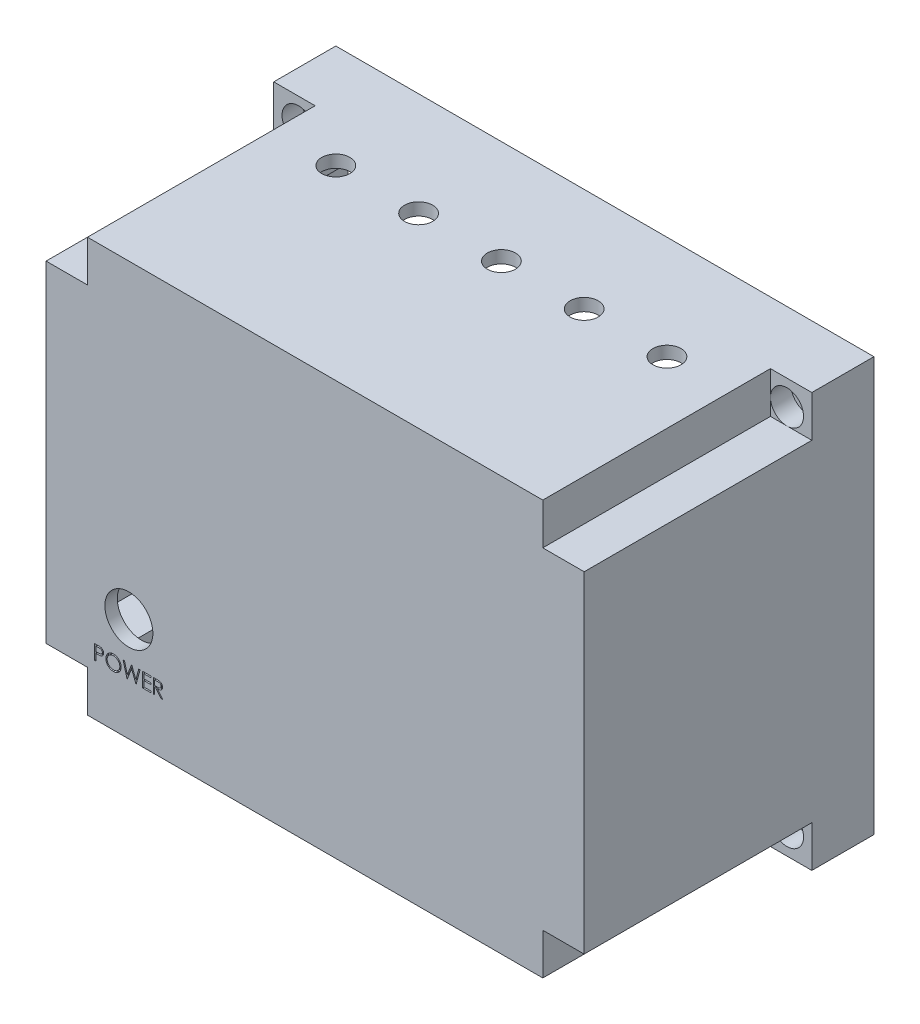
SolidWorks part; units mm, degrees
ref_plane "Front Plane" through (0, 0, 0) normal (0, 0, 1) x (1, 0, 0)
ref_plane "Top Plane" through (0, 0, 0) normal (0, 1, 0) x (1, 0, 0)
ref_plane "Right Plane" through (0, 0, 0) normal (1, 0, 0) x (0, 0, -1)
sketch "Sketch2" plane through (0, 0, 0) normal (0, 1, 0) x (1, 0, 0)
  line L1 (0, 0) -> (130, 0)
  line L2 (0, 0) -> (0, 70)
  line L3 (0, 70) -> (130, 70)
  line L4 (130, 0) -> (130, 70)
  dimension "D1" = 130
  dimension "D2" = 70
extrude "Boss-Extrude1" add sketch "Sketch2" along normal blind 100
sketch "Sketch3" plane through (0, 0, -70) normal (0, 0, -1) x (-1, 0, 0)
  line L0 (-130, 100) -> (0, 100) construction
  line L1 (-117, 87) -> (-13, 87)
  line L2 (-117, 87) -> (-117, 13)
  line L3 (-117, 13) -> (-13, 13)
  line L4 (-13, 87) -> (-13, 13)
  line L5 (-117, 87) -> (-13, 13) construction
  line L6 (-117, 13) -> (-13, 87) construction
  line L7 (-130, 100) -> (-130, 0) construction
  line L8 (-130, 0) -> (0, 0) construction
  line L9 (0, 100) -> (0, 0) construction
  point P0 (-65, 50)
  dimension "D1" = 13
  dimension "D2" = 13
  dimension "D3" = 13
  dimension "D4" = 13
extrude "Cut-Extrude1" cut sketch "Sketch3" against normal blind 67
sketch "Sketch4" plane through (0, 0, 0) normal (0, 0, 1) x (1, 0, 0)
  line L1 (0, 100) -> (10, 100)
  line L2 (0, 100) -> (0, 90)
  line L3 (0, 90) -> (10, 90)
  line L4 (10, 100) -> (10, 90)
  line L5 (130, 100) -> (120, 100)
  line L6 (130, 100) -> (130, 90)
  line L7 (130, 90) -> (120, 90)
  line L8 (120, 100) -> (120, 90)
  line L9 (0, 0) -> (10, 0)
  line L10 (0, 0) -> (0, 10)
  line L11 (0, 10) -> (10, 10)
  line L12 (10, 0) -> (10, 10)
  line L13 (130, 0) -> (120, 0)
  line L14 (130, 0) -> (130, 10)
  line L15 (130, 10) -> (120, 10)
  line L16 (120, 0) -> (120, 10)
  dimension "D1" = 10
  dimension "D2" = 10
  dimension "D3" = 10
  dimension "D4" = 10
  dimension "D5" = 10
  dimension "D6" = 10
  dimension "D7" = 10
  dimension "D8" = 10
extrude "Cut-Extrude2" cut sketch "Sketch4" against normal blind 55
sketch "Sketch5" plane through (0, 0, -70) normal (0, 0, -1) x (-1, 0, 0)
  line L0 (-130, 100) -> (0, 100) construction
  line L1 (-117, 87) -> (-13, 87)
  line L2 (-117, 87) -> (-117, 97)
  line L3 (-117, 97) -> (-13, 97)
  line L4 (-13, 87) -> (-13, 97)
  line L9 (-13, 13) -> (-117, 13)
  line L10 (-13, 13) -> (-13, 3)
  line L11 (-13, 3) -> (-117, 3)
  line L12 (-117, 13) -> (-117, 3)
  line L18 (-130, 0) -> (0, 0) construction
  dimension "D1" = 3
  dimension "D3" = 3
extrude "Cut-Extrude3" cut sketch "Sketch5" against normal blind 67
sketch "Sketch6" plane through (0, 0, -70) normal (0, 0, -1) x (-1, 0, 0)
  line L0 (-117, 97) -> (-117, 3) construction
  line L1 (-117, 87) -> (-127, 87)
  line L2 (-117, 87) -> (-117, 13)
  line L3 (-117, 13) -> (-127, 13)
  line L4 (-127, 87) -> (-127, 13)
  line L5 (-13, 3) -> (-13, 97) construction
  line L6 (-13, 87) -> (-3, 87)
  line L7 (-13, 87) -> (-13, 13)
  line L8 (-13, 13) -> (-3, 13)
  line L9 (-3, 87) -> (-3, 13)
  line L10 (-130, 100) -> (-130, 0) construction
  line L11 (-130, 100) -> (0, 100) construction
  line L12 (-130, 0) -> (0, 0) construction
  line L13 (0, 100) -> (0, 0) construction
  dimension "D1" = 3
  dimension "D2" = 13
  dimension "D3" = 13
  dimension "D4" = 13
  dimension "D5" = 3
  dimension "D6" = 13
extrude "Cut-Extrude4" cut sketch "Sketch6" against normal blind 67
sketch "Sketch9" plane through (0, 0, -70) normal (0, 0, -1) x (-1, 0, 0)
  line L0 (-130, 100) -> (0, 100) construction
  line L1 (-130, 100) -> (-130, 0) construction
  line L2 (0, 100) -> (0, 0) construction
  line L3 (-130, 0) -> (0, 0) construction
  circle A0 centre (-124, 94) radius 1.75
  circle A1 centre (-124, 6) radius 1.75
  circle A2 centre (-6, 94) radius 1.75
  circle A3 centre (-6, 6) radius 1.75
  dimension "D1" = 3.5
  dimension "D4" = 3.5
  dimension "D7" = 3.5
  dimension "D10" = 3.5
  dimension "D2" = 6
  dimension "D3" = 6
  dimension "D5" = 6
  dimension "D6" = 6
  dimension "D8" = 6
  dimension "D9" = 6
  dimension "D11" = 6
  dimension "D12" = 6
extrude "Cut-Extrude5" cut sketch "Sketch9" against normal blind 67
sketch "Sketch10" plane through (0, 0, -55) normal (0, 0, 1) x (1, 0, 0)
  line L0 (130, 100) -> (120, 100) construction
  line L1 (130, 90) -> (130, 100) construction
  circle A0 centre (124, 94) radius 4
  dimension "D3" = 8
  dimension "D1" = 6
  dimension "D2" = 6
extrude "Cut-Extrude6" cut sketch "Sketch10" against normal blind 5
sketch "Sketch12" plane through (0, 0, -55) normal (0, 0, 1) x (1, 0, 0)
  line L0 (130, 0) -> (130, 10) construction
  line L1 (120, 0) -> (130, 0) construction
  circle A0 centre (124, 6) radius 4
  dimension "D3" = 8
  dimension "D1" = 6
  dimension "D2" = 6
extrude "Cut-Extrude7" cut sketch "Sketch12" against normal blind 5
sketch "Sketch13" plane through (0, 0, -55) normal (0, 0, 1) x (1, 0, 0)
  line L0 (0, 0) -> (10, 0) construction
  line L1 (0, 10) -> (0, 0) construction
  circle A0 centre (6, 6) radius 4
  dimension "D3" = 8
  dimension "D1" = 6
  dimension "D2" = 6
extrude "Cut-Extrude8" cut sketch "Sketch13" against normal blind 5
sketch "Sketch14" plane through (0, 0, -55) normal (0, 0, 1) x (1, 0, 0)
  line L0 (0, 100) -> (0, 90) construction
  line L1 (10, 100) -> (0, 100) construction
  circle A0 centre (6, 94) radius 4
  dimension "D3" = 8
  dimension "D1" = 6
  dimension "D2" = 6
extrude "Cut-Extrude9" cut sketch "Sketch14" against normal blind 5
sketch "Sketch15" plane through (0, 0, -70) normal (0, 0, -1) x (-1, 0, 0)
  line L1 (-117, 87) -> (-120, 87)
  line L2 (-117, 87) -> (-117, 90)
  line L3 (-117, 90) -> (-120, 90)
  line L4 (-120, 87) -> (-120, 90)
  line L5 (-117, 13) -> (-120, 13)
  line L6 (-117, 13) -> (-117, 10)
  line L7 (-117, 10) -> (-120, 10)
  line L8 (-120, 13) -> (-120, 10)
  line L9 (-13, 13) -> (-10, 13)
  line L10 (-13, 13) -> (-13, 10)
  line L11 (-13, 10) -> (-10, 10)
  line L12 (-10, 13) -> (-10, 10)
  line L13 (-13, 87) -> (-10, 87)
  line L14 (-13, 87) -> (-13, 90)
  line L15 (-13, 90) -> (-10, 90)
  line L16 (-10, 87) -> (-10, 90)
  dimension "D1" = 3
  dimension "D2" = 3
  dimension "D3" = 3
  dimension "D4" = 3
  dimension "D5" = 3
  dimension "D6" = 3
  dimension "D7" = 3
  dimension "D8" = 3
extrude "Boss-Extrude2" add sketch "Sketch15" along normal blind 5
sketch "Sketch16" plane through (0, 3, 0) normal (0, 1, 0) x (1, 0, 0)
  line L3 (117, 70) -> (41, 70)
  line L4 (117, 70) -> (117, 67)
  line L5 (117, 67) -> (41, 67)
  line L6 (41, 70) -> (41, 67)
  dimension "D1" = 3
  dimension "D2" = 76
extrude "Boss-Extrude3" add sketch "Sketch16" along normal blind 15
sketch "Sketch17" plane through (0, 0, -3) normal (0, 0, -1) x (-1, 0, 0)
  line L0 (-117, 18) -> (-41, 18) construction
  line L1 (-101, 18) -> (-98, 18)
  line L2 (-101, 18) -> (-101, 48)
  line L3 (-101, 48) -> (-98, 48)
  line L4 (-98, 18) -> (-98, 48)
  line L5 (-117, 18) -> (-117, 13) construction
  line L6 (-38, 18) -> (-35, 18)
  line L7 (-38, 18) -> (-38, 48)
  line L8 (-38, 48) -> (-35, 48)
  line L9 (-35, 18) -> (-35, 48)
  dimension "D1" = 30
  dimension "D2" = 30
  dimension "D3" = 3
  dimension "D4" = 3
  dimension "D5" = 16
  dimension "D6" = 60
extrude "Boss-Extrude4" add sketch "Sketch17" along normal blind 15
sketch "Sketch18" plane through (0, 0, -3) normal (0, 0, -1) x (-1, 0, 0)
  line L0 (-130, 0) -> (0, 0) construction
  line L1 (0, 100) -> (0, 0) construction
  circle A0 centre (-20, 25) radius 5.8
  dimension "D1" = 11.6
  dimension "D2" = 25
  dimension "D3" = 20
extrude "Cut-Extrude10" cut sketch "Sketch18" against normal blind 15
sketch "Sketch19" plane through (0, 100, 0) normal (0, 1, 0) x (1, 0, 0)
  line L2 (0, 70) -> (0, 45) construction
  line L3 (0, 55) -> (0, 0) construction
  line L4 (0, 45) -> (130, 45) construction
  line L5 (130, 55) -> (130, 0) construction
  line L6 (10, 55) -> (10, 0) construction
  circle A0 centre (25, 45) radius 3.4
  circle A1 centre (45, 45) radius 3.4
  circle A2 centre (65, 45) radius 3.4
  circle A3 centre (85, 45) radius 3.4
  circle A4 centre (105, 45) radius 3.4
  dimension "D7" = 6.8
  dimension "D8" = 6.8
  dimension "D9" = 6.8
  dimension "D10" = 6.8
  dimension "D11" = 6.8
  dimension "D1" = 25
  dimension "D2" = 15
  dimension "D3" = 95
  dimension "D4" = 75
  dimension "D5" = 55
  dimension "D6" = 35
extrude "Cut-Extrude11" cut sketch "Sketch19" against normal blind 15
sketch "Sketch20" plane through (0, 0, 0) normal (0, 0, 1) x (1, 0, 0)
  text T0 "POWER"
extrude "Cut-Extrude12" cut sketch "Sketch20" against normal blind 0.5
